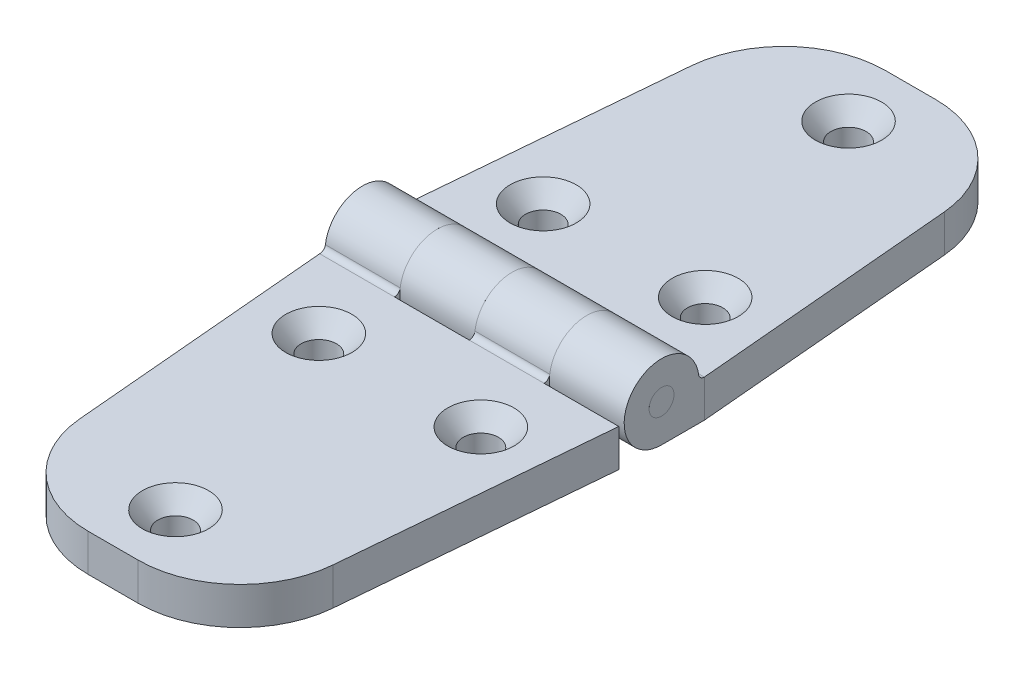
SolidWorks part; units mm, degrees
ref_plane "Front" through (0, 0, 0) normal (0, 0, 1) x (1, 0, 0)
ref_plane "Top" through (0, 0, 0) normal (0, 1, 0) x (1, 0, 0)
ref_plane "Right" through (0, 0, 0) normal (1, 0, 0) x (0, 0, -1)
sketch "Sketch1" plane through (0, 0, 0) normal (1, 0, 0) x (0, 0, -1)
  line L0 (0, 0) -> (-50.8, 0)
  line L1 (-50.8, 0) -> (-50.8, 4.7625)
  line L2 (-50.8, 4.7625) -> (0, 4.7625)
  line L3 (0, 4.7625) -> (50.8, 4.7625)
  line L4 (50.8, 4.7625) -> (50.8, 0)
  line L5 (50.8, 0) -> (0, 0)
  circle A0 centre (0, 4.7625) radius 4.7625
  circle A1 centre (0, 4.7625) radius 1.5875
  dimension "Pin Dia" = 3.175
  dimension "Kn Dia" = 9.525
  dimension "Th" = 4.7625
  dimension "A" = 50.8
sketch "Sketch2" plane through (0, 0, 0) normal (1, 0, 0) x (0, 0, -1)
  line L0 (0, 0) -> (-50.8, 0)
  line L1 (-50.8, 0) -> (-50.8, 4.7625)
  line L2 (-50.8, 4.7625) -> (-5.4461, 4.7625)
  line L3 (-50.8, 4.7625) -> (0, 4.7625) construction
  arc A0 (0, 0) -> (-4.72, 5.3975) centre (0, 4.7625) ccw
  circle A1 centre (0, 4.7625) radius 4.7625 construction
  circle A2 centre (0, 4.7625) radius 1.5875
  circle A3 centre (0, 4.7625) radius 1.5875 construction
  arc A4 (-5.4461, 4.7625) -> (-4.72, 5.3975) centre (-5.4461, 5.4952) ccw
  dimension "D1" = 0.635
extrude "Extrude1" add sketch "Sketch2" along normal mid plane 38.1
sketch "Sketch24" plane through (0, 0, 0) normal (0, 1, 0) x (1, 0, 0)
  line L1 (-9.525, 4.7625) -> (0, 4.7625)
  line L2 (-9.525, 4.7625) -> (-9.525, -5.4461)
  line L3 (-9.525, -5.4461) -> (0, -5.4461)
  line L4 (0, 4.7625) -> (0, -5.4461)
  line L5 (9.525, 4.7625) -> (19.05, 4.7625)
  line L6 (9.525, 4.7625) -> (9.525, -5.4461)
  line L7 (9.525, -5.4461) -> (19.05, -5.4461)
  line L8 (19.05, 4.7625) -> (19.05, -5.4461)
  line L9 (19.05, -0.3418) -> (9.525, -0.3418) construction
  line L10 (9.525, -0.3418) -> (0, -0.3418) construction
  line L11 (0, -0.3418) -> (-9.525, -0.3418) construction
  line L12 (-9.525, -0.3418) -> (-19.05, -0.3418) construction
  line L13 (-19.05, 4.7625) -> (-19.05, -4.72) construction
  line L16 (19.05, -5.4461) -> (-19.05, -5.4461) construction
  line L17 (19.05, 4.7625) -> (-19.05, 4.7625) construction
extrude "Cut-Extrude5" cut sketch "Sketch24" along normal through all
sketch "Sketch4" plane through (0, 0, 0) normal (1, 0, 0) x (0, 0, -1)
  line L0 (0, 0) -> (50.8, 0)
  line L1 (50.8, 0) -> (50.8, 4.7625)
  line L2 (50.8, 4.7625) -> (5.4461, 4.7625)
  line L3 (0, 4.7625) -> (50.8, 4.7625) construction
  arc A0 (0, 0) -> (4.72, 5.3975) centre (0, 4.7625) cw
  circle A1 centre (0, 4.7625) radius 4.7625 construction
  circle A2 centre (0, 4.7625) radius 1.5875
  circle A3 centre (0, 4.7625) radius 1.5875 construction
  arc A4 (4.72, 5.3975) -> (5.4461, 4.7625) centre (5.4461, 5.4952) ccw
  dimension "D1" = 0.635
extrude "Extrude2" add sketch "Sketch4" along normal up to surface and the other way up to surface separate body
sketch "Sketch25" plane through (0, 0, 0) normal (0, 1, 0) x (1, 0, 0)
  line L0 (9.525, 4.7625) -> (9.525, -5.4461) construction
  line L2 (-19.05, 5.4461) -> (-9.525, 5.4461)
  line L3 (-19.05, 5.4461) -> (-19.05, -4.72)
  line L4 (-19.05, -4.72) -> (-9.525, -4.72)
  line L5 (-9.525, 5.4461) -> (-9.525, -4.72)
  line L6 (0, 5.4461) -> (9.525, 5.4461)
  line L7 (0, 5.4461) -> (0, -4.72)
  line L8 (0, -4.72) -> (9.525, -4.72)
  line L9 (19.05, 5.4461) -> (-19.05, 5.4461) construction
  line L10 (-9.525, -4.72) -> (-19.05, -4.72) construction
  line L12 (9.525, 5.4461) -> (9.525, -4.72)
extrude "Cut-Extrude6" cut sketch "Sketch25" along normal through all
ref_plane "Plane1" through (0, 4.7625, 0) normal (0, 1, 0) x (-1, 0, 0)
sketch "Sketch7" plane through (0, 4.7625, 0) normal (0, 1, 0) x (-1, 0, 0)
  line L0 (-19.05, 0) -> (19.05, 0)
  line L1 (-19.05, -1.5875) -> (-19.05, 0)
  line L2 (-19.05, -1.5875) -> (19.05, -1.5875)
  line L3 (19.05, -1.5875) -> (19.05, 0)
  point P5 (0, -1.5875)
revolve "Revolve1" add sketch "Sketch7" angle 360 about L0
sketch "Sketch8" plane through (0, 4.7625, 0) normal (0, 1, 0) x (-1, 0, 0)
  line L0 (-19.05, -5.4461) -> (-16.1198, -38.9383)
  line L1 (19.05, -5.4461) -> (16.1198, -38.9383)
  line L2 (-19.05, -5.4461) -> (-22.1191, -5.4461)
  line L3 (-22.1191, -5.4461) -> (-22.1191, -53.4641)
  line L4 (-22.1191, -53.4641) -> (22.1191, -53.4641)
  line L5 (22.1191, -53.4641) -> (22.1191, -5.4461)
  line L6 (22.1191, -5.4461) -> (19.05, -5.4461)
  line L7 (19.05, -5.4461) -> (19.05, -50.8) construction
  line L10 (-19.05, -50.8) -> (-19.05, -5.4461) construction
  line L11 (3.175, -50.8) -> (-3.175, -50.8)
  line L12 (-19.05, -50.8) -> (19.05, -50.8) construction
  line L13 (3.175, 50.8) -> (-3.175, 50.8)
  line L14 (-19.05, 50.8) -> (19.05, 50.8) construction
  line L15 (9.525, -5.4461) -> (19.05, -5.4461) construction
  line L16 (19.05, 0) -> (-19.05, 0) construction
  line L17 (22.1191, 5.4461) -> (19.05, 5.4461)
  line L18 (22.1191, 53.4641) -> (22.1191, 5.4461)
  line L19 (-22.1191, 53.4641) -> (22.1191, 53.4641)
  line L20 (-22.1191, 5.4461) -> (-22.1191, 53.4641)
  line L21 (-19.05, 5.4461) -> (-22.1191, 5.4461)
  line L22 (19.05, 5.4461) -> (16.1198, 38.9383)
  line L23 (-19.05, 5.4461) -> (-16.1198, 38.9383)
  line L24 (-19.05, -4.7625) -> (-19.05, 5.4461) construction
  arc A1 (3.175, -50.8) -> (16.1198, -38.9383) centre (3.175, -37.8057) ccw
  arc A2 (-3.175, -50.8) -> (-16.1198, -38.9383) centre (-3.175, -37.8057) cw
  arc A3 (16.1198, 38.9383) -> (3.175, 50.8) centre (3.175, 37.8057) ccw
  arc A4 (-16.1198, 38.9383) -> (-3.175, 50.8) centre (-3.175, 37.8057) cw
  point P37 (0, -50.8)
  dimension "D1" = 85
  dimension "D2" = 6.35
extrude "Cut-Extrude4" cut sketch "Sketch8" against normal blind 1056.132
sketch "Sketch9" plane through (0, 4.7625, 0) normal (0, 1, 0) x (-1, 0, 0)
  line L0 (19.05, -4.7625) -> (19.05, 4.72) construction
  line L1 (19.05, 0) -> (-19.05, 0) construction
  line L4 (-19.05, -4.7625) -> (-19.05, 5.4461) construction
  line L5 (0, -50.8) -> (0, 0) construction
  line L6 (3.175, -50.8) -> (-3.175, -50.8) construction
  line L7 (0, -42.8625) -> (0, -50.8) construction
  point P20 (0, -42.8625)
  point P21 (10.3187, -14.2875)
  point P28 (-10.3188, -14.2875)
  point P33 (-10.3188, 14.2875)
  point P34 (10.3187, 14.2875)
  point P35 (0, 42.8625)
  dimension "D1" = 20.6375
  dimension "D2" = 7.9375
  dimension "D3" = 28.575
hole_wizard "CSK for #8 Flat Head Machine Screw1" positions "Sketch14" profile "Sketch13" countersink size "#8" standard "Ansi Inch"
sketch "Sketch14" plane through (-3.1926, 4.7625, 34.0762) normal (0, 1, 0) x (-1, 0, 0)
  point P31 (-3.1926, -76.9387)
  point P34 (7.1262, -48.3637)
  point P37 (-13.5113, -48.3637)
  point P40 (7.1262, -19.7887)
  point P43 (-13.5113, -19.7887)
  point P46 (-3.1926, 8.7863)
sketch "Sketch13" plane through (0, 4.7625, -42.8625) normal (1, 0, 0) x (0, 0, 1)
  line L0 (0, 0) -> (0, 4.7625)
  line L1 (0, 4.7625) -> (2.2479, 4.7625)
  line L2 (2.2479, 4.7625) -> (2.2479, 2.2645)
  line L3 (2.2479, 2.2645) -> (4.2164, 0)
  line L5 (4.2164, 0) -> (0, 0)
  line L6 (-2.2479, 2.2645) -> (-4.2164, 0) construction
  line L11 (0, -6.35) -> (0, 107.95) construction
  dimension "Thru Hole Dia." = 4.4958
  dimension "Thru Hole Depth" = 4.7625
  dimension "Near C'Sink Dia." = 8.4328
  dimension "Near C'Sink Angle" = 82
